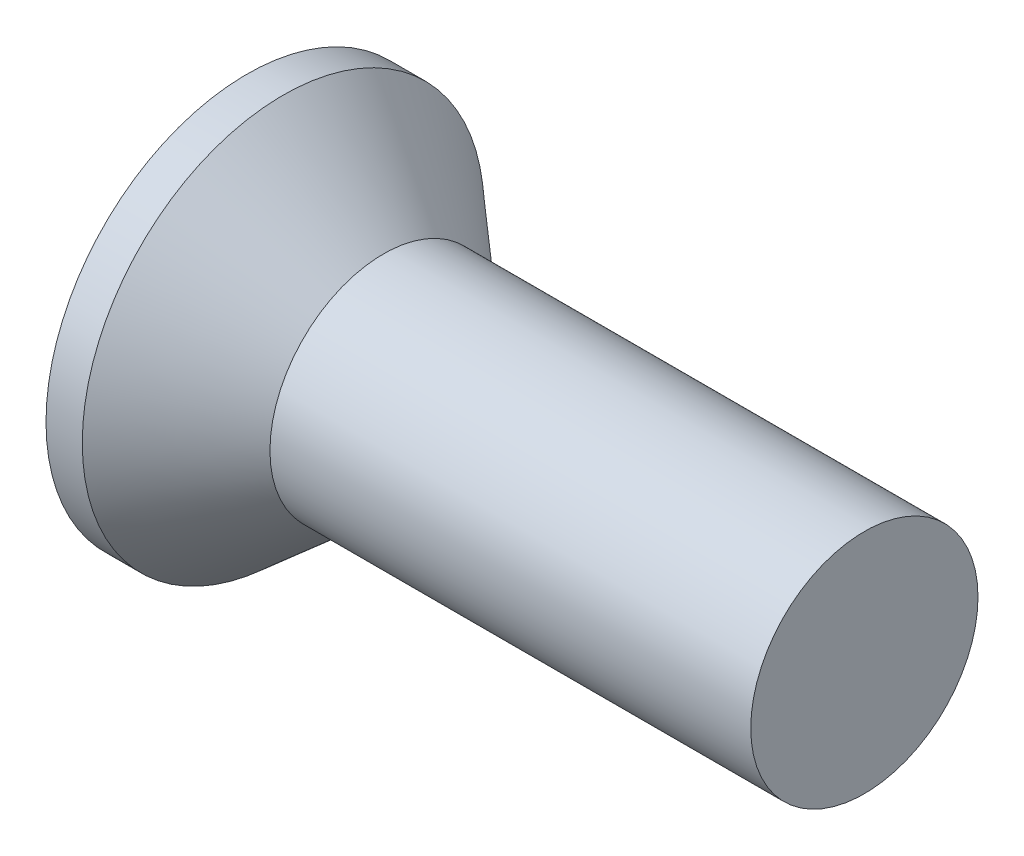
SolidWorks part; units mm, degrees
revolve "Base-Revolve" add sketch "BodySke" angle 360 about L5
sketch "BodySke" plane through (0, 0, 0) normal (0, 0, 1) x (1, 0, 0)
  line L0 (0, 0) -> (0, 3.0988)
  line L1 (0, 3.0988) -> (0.5596, 3.0988)
  line L2 (2.1082, 1.7526) -> (9.525, 1.7526)
  line L3 (9.525, 1.7526) -> (9.525, 0)
  line L4 (9.525, 0) -> (0, 0)
  line L5 (-6.35, 0) -> (82.55, 0) construction
  line L6 (2.1082, -1.7526) -> (9.525, -1.7526) construction
  line L7 (0.5596, -3.0988) -> (2.1082, -1.7526) construction
  line L8 (0.5596, 3.0988) -> (2.1082, 1.7526)
  line L9 (0, -3.0988) -> (0.5596, -3.0988) construction
  line L10 (2.9007, 3.3401) -> (2.9007, -6.1849) construction
  line L11 (0, 6.35) -> (0, -3.175) construction
  dimension "Diameter" = 3.5052
  dimension "Length" = 9.525
  dimension "Head_ht" = 2.1082
  dimension "Head_dia" = 6.1976
  dimension "Head_ang" = 82
  dimension "D6" = 0.5596
  dimension "Advance" = 0.7925
  dimension "Thread_nom" = 9.525
cosmetic thread "ThreadCosmetic" [suppressed] parameters "Thread_length"=6.6243, "Thread_minor"=2.5603
extrude "Slot" [suppressed] cut sketch "Sketch2" against normal blind 0.9652
sketch "Sketch2" plane through (0, 0, 0) normal (-1, 0, 0) x (0, 0, 1)
  line L0 (-3.0988, -0.6096) -> (3.0988, -0.6096)
  line L1 (-3.0988, -0.6096) -> (-3.0988, 0.6096)
  line L2 (3.0988, 0.6096) -> (-3.0988, 0.6096)
  line L3 (3.0988, 0.6096) -> (3.0988, -0.6096)
  dimension "Slot_width" = 1.2192
  dimension "D1" = 0.6096
  dimension "D2" = 6.1976
  dimension "D3" = 3.0988
material "Cast Alloy Steel"
ref_plane "Plane1" through (0, 0, 0) normal (0, 0, 1) x (1, 0, 0)
ref_plane "Plane2" through (0, 0, 0) normal (0, 1, 0) x (1, 0, 0)
ref_plane "Plane3" through (0, 0, 0) normal (1, 0, 0) x (0, 0, -1)
sketch "Sketch3" plane through (0, 0, 0) normal (-1, 0, 0) x (0, 0, 1)
  line L0 (-0.4826, 2.4765) -> (0.4826, 2.4765)
  line L1 (0.4826, 2.4765) -> (0.4826, -2.4765)
  line L2 (0.4826, -2.4765) -> (-0.4826, -2.4765)
  line L3 (-0.4826, -2.4765) -> (-0.4826, 2.4765)
  dimension "Cross_dia" = 4.953
  dimension "Cross_width" = 0.9652
  dimension "D1" = 2.4765
  dimension "D2" = 0.4826
ref_plane "Plane4" through (2.8702, 0, 0) normal (-1, 0, 0) x (0, 0, 1)
sketch "Sketch4" plane through (2.8702, 0, 0) normal (-1, 0, 0) x (0, 0, 1)
  line L0 (-0.2413, 0.2413) -> (0.2413, 0.2413)
  line L3 (0.2413, 0.2413) -> (0.2413, -0.2413)
  line L4 (0.2413, -0.2413) -> (-0.2413, -0.2413)
  line L5 (-0.2413, -0.2413) -> (-0.2413, 0.2413)
  dimension "D2" = 0.4826
  dimension "D1" = 0.4826
  dimension "D3" = 0.2413
  dimension "D4" = 0.2413
loft "Cross" cut profiles "Sketch3", "Sketch4"
pattern_circular "CirPattern1" count 2 every 90 about axis through (0, 0, 0) along (1, 0, 0) of "Cross"
sketch "ThdSchSke" plane through (0, 0, 0) normal (0, 0, 1) x (1, 0, 0)
  line L0 (2.9007, -1.2802) -> (2.5699, -1.7526)
  line L1 (2.9007, -1.2802) -> (3.2315, -1.7526)
  line L2 (3.2315, -1.7526) -> (3.2315, -2.1908)
  line L3 (-3.175, 0) -> (5.1513, 0) construction
  line L5 (3.2315, -2.1908) -> (2.5699, -2.1908)
  line L6 (2.5699, -2.1908) -> (2.5699, -1.7526)
  line L7 (0, 3.0988) -> (0, -3.0988) construction
  dimension "Diameter" = 3.5052
  dimension "Thread_minor" = 2.5603
  dimension "Start" = 2.9007
revolve "ThreadSchematic" [suppressed] cut sketch "ThdSchSke" angle 360 about L3
pattern_linear "ThdSchPat" [suppressed]
equation "\"D1@Sketch3\" = \"Cross_dia@Sketch3\" / 2"
equation "\"D2@Sketch3\" = \"Cross_width@Sketch3\" / 2"
equation "\"D1@Sketch4\" = \"Cross_width@Sketch3\" *.5"
equation "\"D2@Sketch4\" = \"D1@Sketch4\""
equation "\"D4@Sketch4\" = \"D2@Sketch4\" / 2"
equation "\"D3@Sketch4\" = \"D1@Sketch4\" / 2"
equation "\"D1@Sketch2\" = \"Slot_width@Sketch2\" / 2"
equation "\"D2@Sketch2\" = \"Head_dia@BodySke\""
equation "\"D3@Sketch2\" = \"D2@Sketch2\" / 2"
equation "\"Thread_length@ThreadCosmetic\" = ((sgn( (\"Length@BodySke\" - \"Advance@BodySke\" - \"Head_ht@BodySke\" ) - \"Thread_nom@BodySke\" )-1)*( (\"Length@BodySke\" - \"Advance@BodySke\" - \"Head_ht@BodySke\" ) - \"Thread_nom@BodySke\" ))/-2+ \"Thread_nom@BodySke\""
equation "\"Thread_minor@ThdSchSke\" = \"Thread_minor@ThreadCosmetic\""
equation "\"Diameter@ThdSchSke\" = \"Diameter@BodySke\""
equation "\"Overcut@ThdSchSke\" = \"Diameter@BodySke\" * 1.25"
equation "\"Start@ThdSchSke\" = 0.000001 + \"Length@BodySke\" - \"Thread_length@ThreadCosmetic\"  '---Countersunk---"
equation "\"Num_threads@ThdSchPat\" = int( \"Thread_length@ThreadCosmetic\" / \"Advance@BodySke\" + 0.999 )  + 1"
equation "\"Advance@ThdSchPat\" = \"Thread_length@ThreadCosmetic\" /  (\"Num_threads@ThdSchPat\" - 1) 'relax it"
